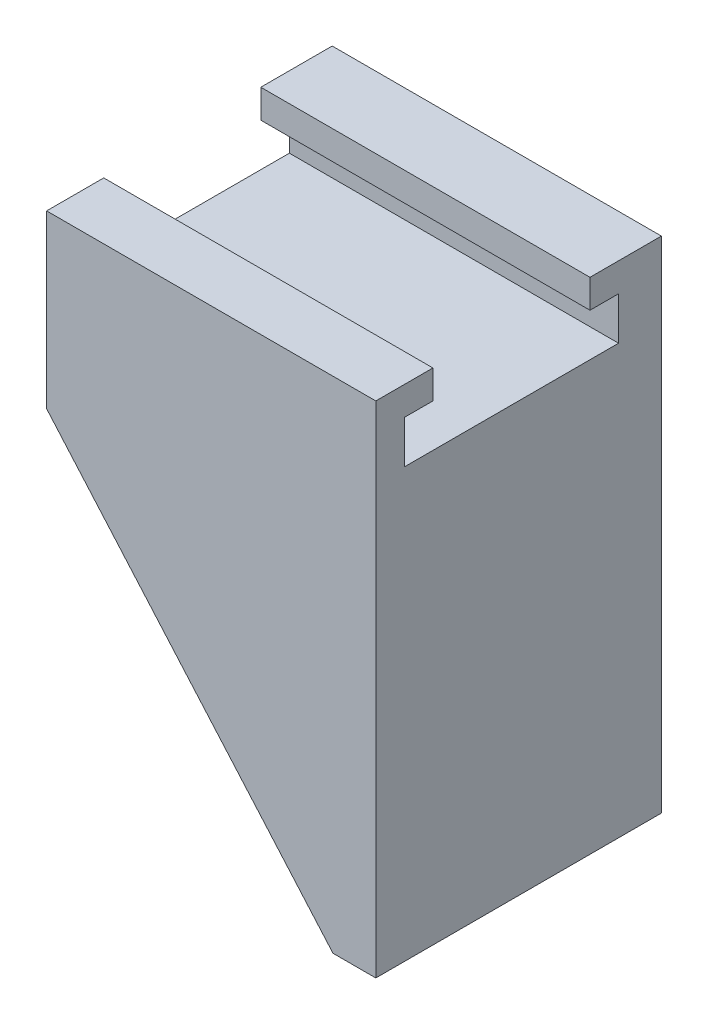
SolidWorks part; units mm, degrees
ref_plane "Front Plane" through (0, 0, 0) normal (0, 0, 1) x (1, 0, 0)
ref_plane "Top Plane" through (0, 0, 0) normal (0, 1, 0) x (1, 0, 0)
ref_plane "Right Plane" through (0, 0, 0) normal (1, 0, 0) x (0, 0, -1)
sketch "Sketch1" plane through (0, 0, 0) normal (0, 0, 1) x (1, 0, 0)
  line L0 (0, 0) -> (3, 0)
  line L1 (3, 0) -> (3, 42)
  line L2 (3, 42) -> (-20.0539, 42)
  line L3 (-20.0539, 42) -> (-20.0539, 23)
  line L4 (-20.0539, 23) -> (0, 0)
  line L5 (-31.0782, 35) -> (30.7097, 35)
  line L6 (-33.3427, 38) -> (28.1218, 38)
  line L7 (-33.3427, 40) -> (28.1218, 40)
  dimension "D1" = 3
  dimension "D2" = 42
  dimension "D3" = 19
  dimension "D4" = 35
  dimension "D5" = 38
  dimension "D6" = 40
extrude "Boss-Extrude1" add sketch "Sketch1" along normal blind 20 contours L5 L3 L4 L0 L1
sketch "Sketch2" plane through (3, 0, 0) normal (1, 0, 0) x (0, 0, -1)
  line L0 (0, 35) -> (-5, 35)
  line L1 (-20, 35) -> (0, 35) construction
  line L2 (-5, 35) -> (-5, 33)
  line L3 (-5, 33) -> (-3, 33)
  line L4 (-3, 33) -> (-3, 30)
  line L5 (-3, 30) -> (-18, 30)
  line L6 (-10.5, 38.2606) -> (-10.5, 9.8868) construction
  line L7 (-20, 0) -> (-20, 35) construction
  line L8 (0, 0) -> (0, 35) construction
  line L9 (-20, 0) -> (-20, 35)
  line L10 (0, 0) -> (0, 35)
  line L11 (-16, 35) -> (-16, 33)
  line L12 (-16, 33) -> (-18, 33)
  line L13 (-18, 33) -> (-18, 30)
  point P14 (-10.5, 30)
  line M9 (0, 35) -> (-20, 35)
  dimension "D1" = 20
  dimension "D2" = 3
  dimension "D3" = 2
  dimension "D4" = 2
  dimension "D5" = 3
  dimension "D6" = 7.5
extrude "Cut-Extrude1" cut sketch "Sketch2" against normal through all contours L6 L11 L12 L13 L5 M9 | L6 L5 L4 L3 L2 M9
